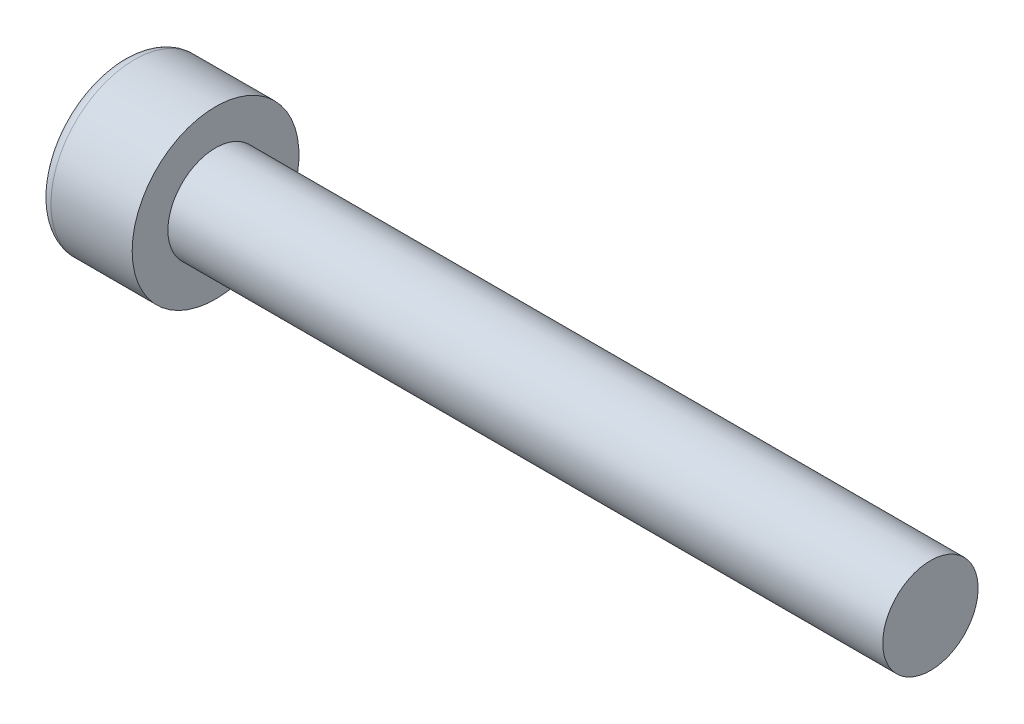
SolidWorks part; units mm, degrees
material "AISI 304"
ref_plane "前视基准面" through (0, 0, 0) normal (0, 0, 1) x (1, 0, 0)
ref_plane "上视基准面" through (0, 0, 0) normal (0, 1, 0) x (1, 0, 0)
ref_plane "右视基准面" through (0, 0, 0) normal (1, 0, 0) x (0, 0, -1)
sketch "草图1" plane through (0, 0, 0) normal (0, 0, 1) x (1, 0, 0)
  line L0 (0, 0) -> (9.1986, 0) construction
  line L1 (0, 0) -> (0, 3.5)
  line L2 (0, 3.5) -> (3.91, 3.5)
  line L3 (3.91, 3.5) -> (3.91, 2)
  line L4 (3.91, 2) -> (33.91, 2)
  line L5 (33.91, 2) -> (33.91, 0)
  line L6 (33.91, 0) -> (0, 0)
  dimension "D1" = 4
  dimension "长度" = 30
  dimension "D2" = 3.91
  dimension "D3" = 7
revolve "旋转1" add sketch "草图1" angle 360 about L0
cosmetic thread "装饰螺纹线1" parameters "D2"=3.242
sketch "草图2" plane through (0, 0, 0) normal (-1, 0, 0) x (0, 0, 1)
  line L1 (-1.7321, 0) -> (-0.866, -1.5)
  line L2 (-0.866, -1.5) -> (0.866, -1.5)
  line L3 (0.866, -1.5) -> (1.7321, 0)
  line L4 (1.7321, 0) -> (0.866, 1.5)
  line L5 (0.866, 1.5) -> (-0.866, 1.5)
  line L6 (-0.866, 1.5) -> (-1.7321, 0)
  circle A0 centre (0, 0) radius 1.5 construction
  dimension "D1" = 3
extrude "切除-拉伸1" cut sketch "草图2" against normal blind 2
fillet "圆角1" radius 0.5 1 edges at (0, 0, 3.5)
